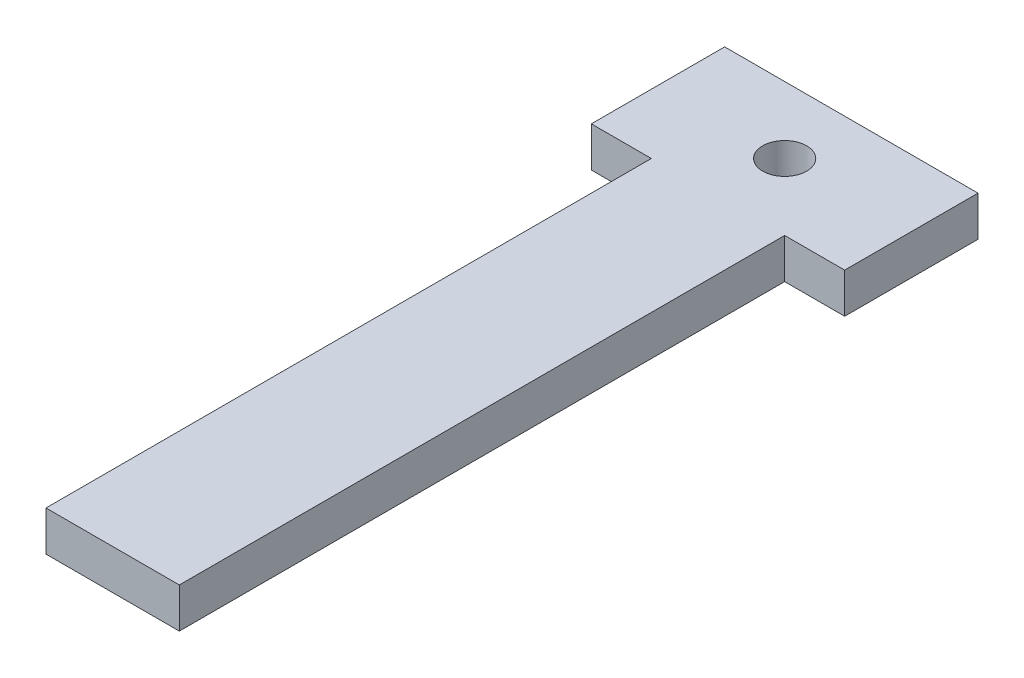
SolidWorks part; units mm, degrees
ref_plane "Front Plane" through (0, 0, 0) normal (0, 0, 1) x (1, 0, 0)
ref_plane "Top Plane" through (0, 0, 0) normal (0, 1, 0) x (1, 0, 0)
ref_plane "Right Plane" through (0, 0, 0) normal (1, 0, 0) x (0, 0, -1)
sketch "Sketch1" plane through (0, 0, 0) normal (0, 1, 0) x (1, 0, 0)
  line L0 (-5, -50.4) -> (5, -50.4)
  line L1 (5, -50.4) -> (5, 5)
  line L4 (5, 5) -> (-5, 5)
  line L5 (-5, 5) -> (-5, -50.4)
  line L7 (9.5, -5) -> (5, -5)
  line L8 (9.5, -5) -> (9.5, 5)
  line L9 (9.5, 5) -> (5, 5)
  line L10 (5, -5) -> (5, 5)
  line L11 (9.5, -5) -> (5, 5) construction
  line L12 (9.5, 5) -> (5, -5) construction
  line L13 (-9.5, -5) -> (-5, -5)
  line L14 (-9.5, -5) -> (-9.5, 5)
  line L15 (-9.5, 5) -> (-5, 5)
  line L16 (-5, -5) -> (-5, 5)
  line L17 (-9.5, -5) -> (-5, 5) construction
  line L18 (-9.5, 5) -> (-5, -5) construction
  circle A0 centre (0, 0) radius 1.65
  point P4 (-7.25, 0)
  point P5 (7.25, 0)
  point P10 (0, -50.4)
  dimension "D3" = 3.3
  dimension "D1" = 10
  dimension "D2" = 55.4
  dimension "D4" = 5
  dimension "D5" = 4.5
  dimension "D6" = 10
extrude "Boss-Extrude1" add sketch "Sketch1" along normal blind 3 contours L4 L5 L0 L1 A0 | L15 L14 L13 L5 | L8 L9 L1 L7
